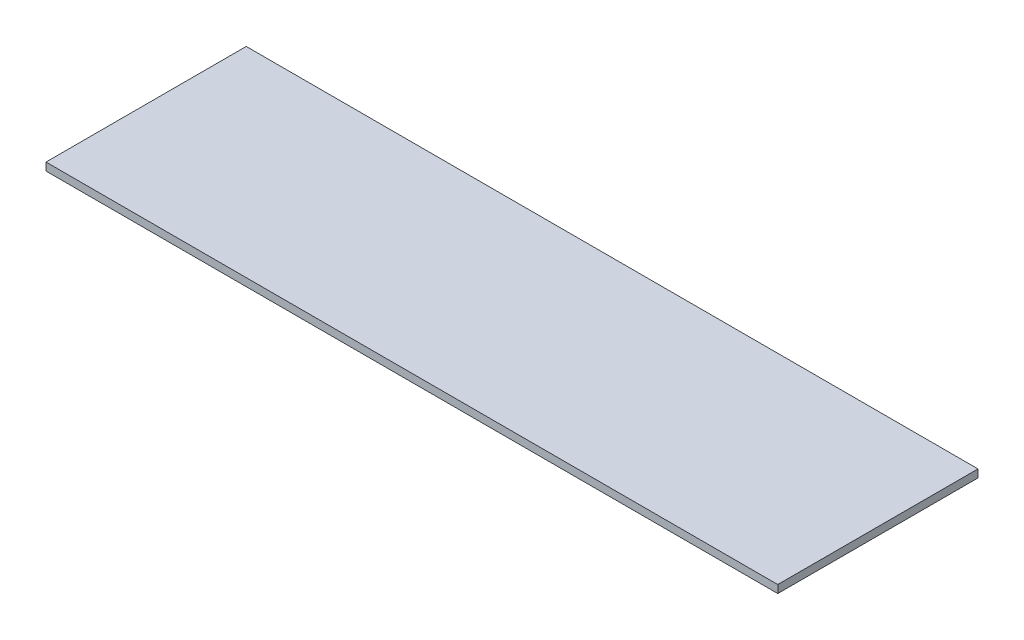
SolidWorks part; units mm, degrees
ref_plane "Front Plane" through (0, 0, 0) normal (0, 0, 1) x (1, 0, 0)
ref_plane "Top Plane" through (0, 0, 0) normal (0, 1, 0) x (1, 0, 0)
ref_plane "Right Plane" through (0, 0, 0) normal (1, 0, 0) x (0, 0, -1)
sketch "Sketch1" plane through (0, 0, 0) normal (0, 1, 0) x (1, 0, 0)
  line L1 (0, 0) -> (279.7556, 0)
  line L2 (0, 0) -> (0, -76.5556)
  line L3 (0, -76.5556) -> (279.7556, -76.5556)
  line L4 (279.7556, 0) -> (279.7556, -76.5556)
  dimension "D1" = 279.7556
  dimension "D2" = 76.5556
extrude "Boss-Extrude1" add sketch "Sketch1" along normal blind 2.9972
